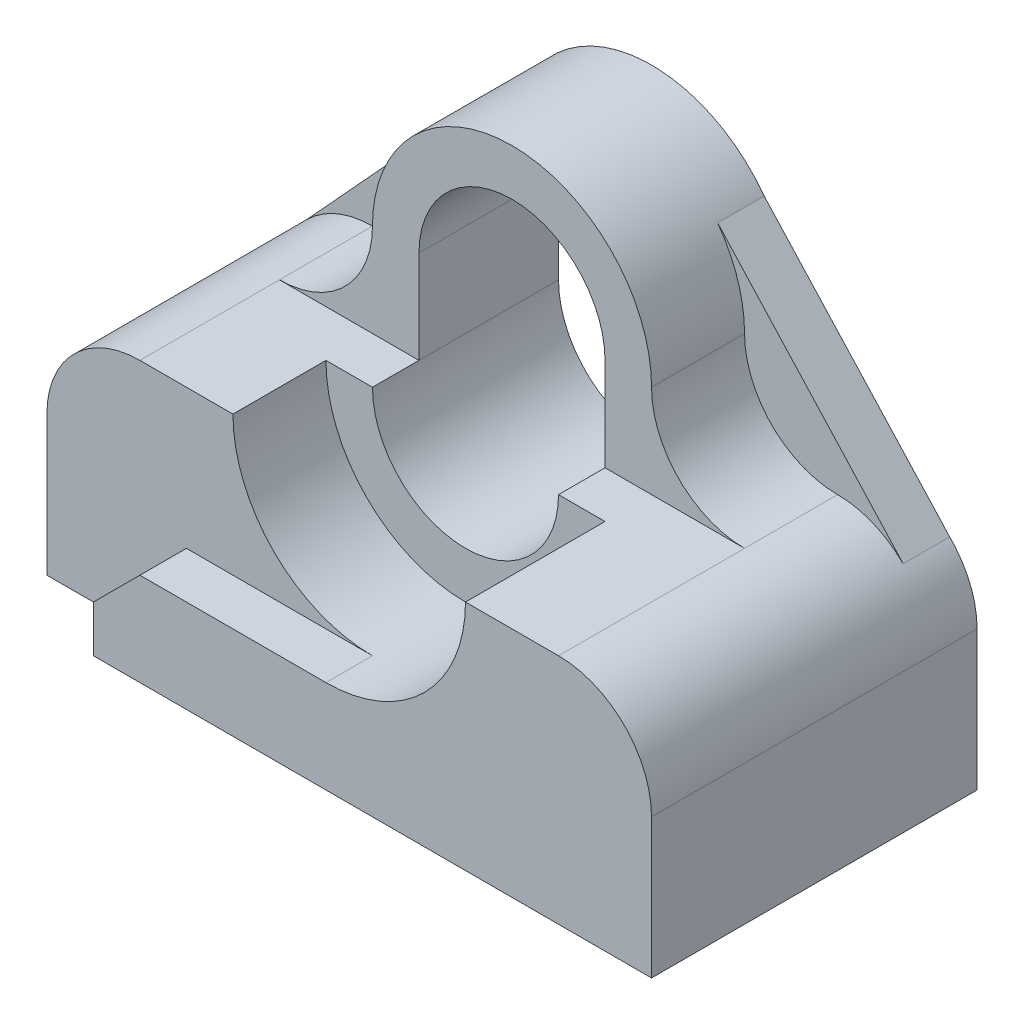
SolidWorks part; units mm, degrees
ref_plane "Front" through (0, 0, 0) normal (0, 0, 1) x (1, 0, 0)
ref_plane "Top" through (0, 0, 0) normal (0, 1, 0) x (1, 0, 0)
ref_plane "Right" through (0, 0, 0) normal (1, 0, 0) x (0, 0, -1)
sketch "Sketch1" plane through (0, 0, 0) normal (0, 0, 1) x (1, 0, 0)
  line L0 (0, 0) -> (0, 2) construction
  line L3 (0, 0) -> (0, 2) construction
  line L4 (-2, 0) -> (-2, 2)
  line L5 (2, 0) -> (2, 2)
  line L6 (-7, -2) -> (-7, -5)
  line L7 (7, -2) -> (7, -5)
  line L8 (-7, -5) -> (7, -5)
  arc A1 (3, 2) -> (-3, 2) centre (0, 2) ccw
  arc A2 (-2, 0) -> (2, 0) centre (0, 0) ccw
  arc A3 (2, 2) -> (-2, 2) centre (0, 2) ccw
  arc A4 (-3, 2) -> (-5, 0) centre (-5, 2) cw
  arc A5 (-5, 0) -> (-7, -2) centre (-5, -2) ccw
  arc A6 (5, 0) -> (7, -2) centre (5, -2) cw
  arc A7 (3, 2) -> (5, 0) centre (5, 2) ccw
  point P3 (0, 1)
  point P8 (0, 1)
  dimension "D3" = 2
  dimension "D6" = 2
  dimension "D9" = 2
  dimension "D1" = 2
  dimension "D4" = 2
  dimension "D5" = 2
  dimension "D7" = 2
  dimension "D8" = 2
  dimension "D10" = 3
extrude "Boss-Extrude1" add sketch "Sketch1" along normal blind 7
sketch "Sketch2" plane through (0, 0, 0) normal (0, 0, -1) x (-1, 0, 0)
  line L0 (0, 0) -> (0, 2) construction
  line L1 (-2, 0) -> (-2, 2)
  line L2 (2, 0) -> (2, 2)
  line L3 (0, 0) -> (0, 2) construction
  line L6 (6.5351, -0.718) -> (2.4215, 3.7709)
  line L7 (7, -5) -> (-7, -5)
  line L8 (7, -5) -> (7, -2)
  line L10 (-7, -5) -> (-7, -2)
  line L11 (0, 2) -> (0, 3.0507) construction
  line L12 (-6.5351, -0.718) -> (-2.4215, 3.7709)
  arc A0 (-2, 0) -> (2, 0) centre (0, 0) ccw
  arc A1 (2, 2) -> (-2, 2) centre (0, 2) ccw
  arc A3 (2.4215, 3.7709) -> (-2.4215, 3.7709) centre (0, 2) ccw
  arc A4 (-6.4108, -0.5824) -> (-7, -2) centre (-5, -2) ccw
  arc A5 (7, -2) -> (6.4108, -0.5824) centre (5, -2) ccw
  point P4 (0, 1)
  point P9 (0, 1)
  arc M15 (5, 0) -> (3, 2) centre (5, 2) cw
  arc M16 (3, 2) -> (-3, 2) centre (0, 2) ccw
  arc M17 (-3, 2) -> (-5, 0) centre (-5, 2) cw
  arc M18 (-5, 0) -> (-7, -2) centre (-5, -2) ccw
  line M19 (-7, -2) -> (-7, -5)
  line M20 (-7, -5) -> (7, -5)
  line M21 (7, -5) -> (7, -2)
  arc M22 (7, -2) -> (5, 0) centre (5, -2) ccw
  line M23 (2, 2) -> (2, 0)
  arc M24 (2, 0) -> (-2, 0) centre (0, 0) cw
  line M25 (-2, 0) -> (-2, 2)
  arc M26 (-2, 2) -> (2, 2) centre (0, 2) cw
  dimension "D1" = 3
  dimension "D2" = 2
  dimension "D3" = 2
extrude "Boss-Extrude2" add sketch "Sketch2" against normal blind 1 contours L12 L6 M18 M19 M20 M21 M22 M15 M16 M17 M26 M23 M24 M25 | L6 M22 M16 M15 | L12 M18 M17 M16
sketch "Sketch3" plane through (0, 0, 7) normal (0, 0, 1) x (1, 0, 0)
  line L1 (-5, 0) -> (5.9748, 0)
  line L2 (-5, 0) -> (-5, 5.6187)
  line L3 (-5, 5.6187) -> (5.9748, 5.6187)
  line L4 (5.9748, 0) -> (5.9748, 5.6187)
extrude "Cut-Extrude1" cut sketch "Sketch3" against normal blind 4
sketch "Sketch4" plane through (0, 0, 7) normal (0, 0, 1) x (1, 0, 0)
  line L0 (0, 2) -> (0, 0) construction
  line L1 (2, 2) -> (2, 0)
  line L2 (-2, 2) -> (-2, 0)
  line L3 (0, 2) -> (0, 0) construction
  line L4 (3, 2) -> (3, 0)
  line L5 (-3, 2) -> (-3, 0)
  arc A0 (2, 2) -> (-2, 2) centre (0, 2) ccw
  arc A1 (-2, 0) -> (2, 0) centre (0, 0) ccw
  arc A2 (3, 2) -> (-3, 2) centre (0, 2) ccw
  arc A3 (-3, 0) -> (3, 0) centre (0, 0) ccw
  point P4 (0, 1)
  point P9 (0, 1)
  dimension "D1" = 3
  dimension "D2" = 2
extrude "Cut-Extrude2" cut sketch "Sketch4" against normal blind 3 contours L5 A3 L4 A2
sketch "Sketch5" plane through (0, 0, 7) normal (0, 0, 1) x (1, 0, 0)
  line L0 (0, -3) -> (-4, -3)
  line L1 (-4, -3) -> (-5, -4)
  line L2 (-5, -4) -> (-5, -5)
  line L3 (-7, -5) -> (7, -5) construction
  line L4 (-5, -5) -> (-7, -5)
  line L5 (-7, -5) -> (-7, 0)
  line L6 (-7, 0) -> (0, 0)
  line L7 (0, 0) -> (0, -3)
  arc A0 (-3, 0) -> (3, 0) centre (0, 0) ccw construction
  dimension "D1" = 4
  dimension "D2" = 1
  dimension "D3" = 1
  dimension "D4" = 1
extrude "Cut-Extrude3" cut sketch "Sketch5" against normal blind 1
